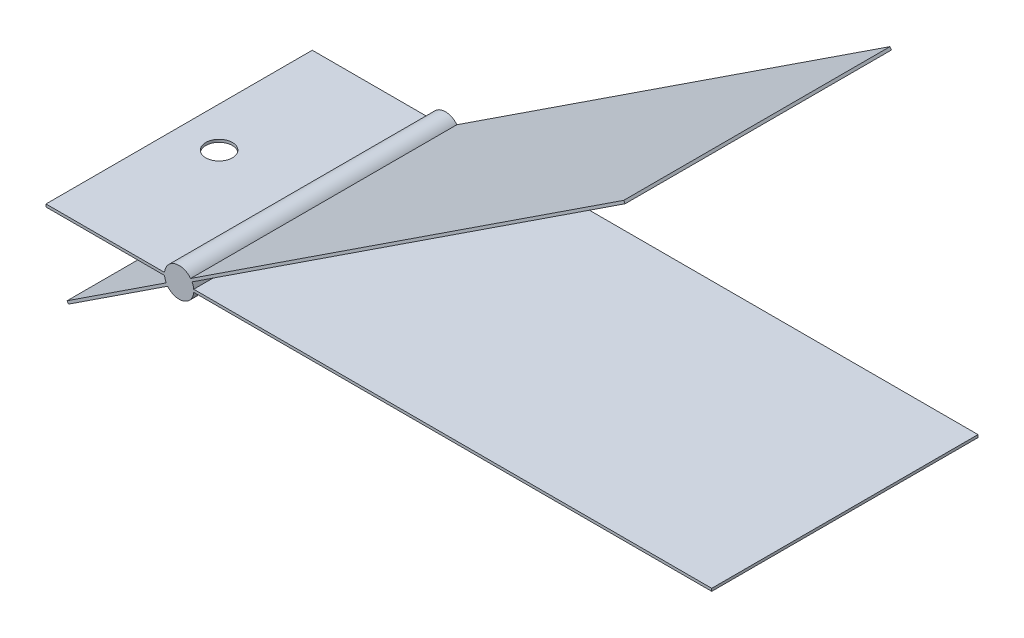
SolidWorks part; units mm, degrees
ref_plane "前视基准面" through (0, 0, 0) normal (0, 0, 1) x (1, 0, 0)
ref_plane "上视基准面" through (0, 0, 0) normal (0, 1, 0) x (1, 0, 0)
ref_plane "右视基准面" through (0, 0, 0) normal (1, 0, 0) x (0, 0, -1)
sketch "草图1" plane through (0, 0, 0) normal (0, 0, 1) x (1, 0, 0)
  line L0 (1.0954, 0.1) -> (40, 0.1)
  line L2 (1.0954, -0.1) -> (40, -0.1)
  line L3 (-10, -0.1) -> (-1.0954, -0.1)
  line L4 (-8.3059, -5.5697) -> (-0.861, -0.6846)
  line L6 (-10, 0.1) -> (-1.0954, 0.1)
  line L7 (-8.4156, -5.4025) -> (-0.9707, -0.5174)
  line L8 (0.861, 0.6846) -> (33.3882, 22.0281)
  line L9 (-10, 0.1) -> (-10, -0.1)
  line L10 (-8.4156, -5.4025) -> (-8.3059, -5.5697)
  line L11 (33.3882, 22.0281) -> (33.498, 21.8608)
  line L12 (40, 0.1) -> (40, -0.1)
  line L28 (0.9707, 0.5174) -> (33.498, 21.8608)
  arc A0 (0.861, 0.6846) -> (-1.0954, 0.1) centre (0, 0) ccw
  arc A1 (-1.0954, -0.1) -> (-0.9707, -0.5174) centre (0, 0) ccw
  arc A3 (1.0954, 0.1) -> (0.9707, 0.5174) centre (0, 0) ccw
  arc A5 (-0.861, -0.6846) -> (1.0954, -0.1) centre (0, 0) ccw
extrude "凸台-拉伸1" add sketch "草图1" along normal blind 20
sketch "草图2" plane through (0, 0.1, 0) normal (0, 1, 0) x (1, 0, 0)
  line L0 (-10, -10) -> (-1.0954, -10)
  line L1 (-10, -20) -> (-10, 0) construction
  line L2 (-1.0954, -20) -> (-1.0954, 0) construction
  circle A0 centre (-7, -10) radius 1
  dimension "D2" = 2
  dimension "D1" = 3
extrude "切除-拉伸1" cut sketch "草图2" against normal blind 1 and the other way blind 20 contours L0 A0 | L0 A0
sketch "草图3" plane through (0.0549, -0.0836, 0) normal (0.5486, -0.8361, 0) x (0.8361, 0.5486, 0)
  line L0 (-10, 10) -> (-1.0954, 10)
  line L1 (-10, 20) -> (-10, 0) construction
  line L2 (-1.0954, 20) -> (-1.0954, 0) construction
  circle A0 centre (-7, 10) radius 1
  dimension "D2" = 2
  dimension "D1" = 3
extrude "切除-拉伸2" cut sketch "草图3" against normal blind 1 contours L0 A0 | L0 A0
